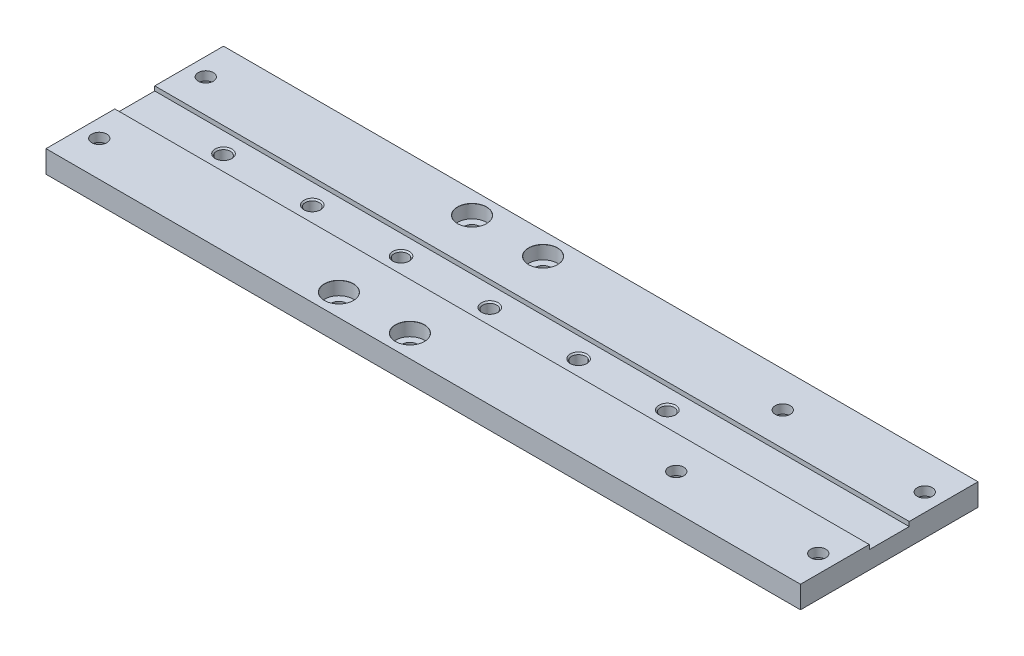
SolidWorks part; units mm, degrees
material "Liga 6061"
ref_plane "Plano frontal" through (0, 0, 0) normal (0, 0, 1) x (1, 0, 0)
ref_plane "Plano superior" through (0, 0, 0) normal (0, 1, 0) x (1, 0, 0)
ref_plane "Plano direito" through (0, 0, 0) normal (1, 0, 0) x (0, 0, -1)
sketch "Esboço1" plane through (0, 0, 0) normal (0, 1, 0) x (1, 0, 0)
  line L1 (85, -20) -> (-85, -20)
  line L2 (85, -20) -> (85, 20)
  line L3 (85, 20) -> (-85, 20)
  line L4 (-85, -20) -> (-85, 20)
  line L5 (85, -20) -> (-85, 20) construction
  line L6 (85, 20) -> (-85, -20) construction
  point P0 (0, 0)
  dimension "D1" = 40
  dimension "D2" = 170
extrude "Ressalto-extrusão1" add sketch "Esboço1" along normal blind 5
sketch "Esboço2" plane through (0, 5, 0) normal (0, 1, 0) x (1, 0, 0)
  line L0 (-85, 20) -> (-85, -20) construction
  line L1 (85, -4.5) -> (-85, -4.5)
  line L2 (85, -4.5) -> (85, 4.5)
  line L3 (85, 4.5) -> (-85, 4.5)
  line L4 (-85, -4.5) -> (-85, 4.5)
  line L5 (85, -4.5) -> (-85, 4.5) construction
  line L6 (85, 4.5) -> (-85, -4.5) construction
  point P0 (0, 0)
  dimension "D1" = 9
extrude "Corte-extrusão1" cut sketch "Esboço2" against normal blind 1
hole_wizard "Rebaixo para SHCS M31" positions "Esboço3" profile "Esboço4" counterbore size "M3" standard "Ansi Metric" end condition through all
sketch "Esboço3" plane through (0, 0, 0) normal (0, -1, 0) x (-1, 0, 0)
  line L0 (-85, -20) -> (-85, 20) construction
  line L1 (-85, 20) -> (85, 20) construction
  line L2 (85, -20) -> (-85, -20) construction
  line L3 (85, 20) -> (85, -20) construction
  point P0 (81, 12)
  point P2 (81, -12)
  point P4 (-49, 12)
  point P6 (-49, -12)
  point P8 (-81, 12)
  point P10 (-81, -12)
  dimension "D1" = 4
  dimension "D2" = 8
  dimension "D3" = 4
  dimension "D4" = 8
  dimension "D5" = 4
  dimension "D6" = 4
  dimension "D7" = 8
  dimension "D8" = 8
  dimension "D9" = 134
  dimension "D10" = 8
  dimension "D11" = 134
  dimension "D12" = 8
sketch "Esboço4" plane through (-81, 0, -12) normal (1, 0, 0) x (0, 0, -1)
  line L0 (0, 0) -> (0, 5)
  line L1 (0, 5) -> (1.7, 5)
  line L3 (1.7, 5) -> (1.7, 3)
  line L4 (3.25, 3) -> (1.7, 3)
  line L5 (3.25, 3) -> (3.25, 0.025)
  line L6 (3.25, 0.025) -> (3.275, 0)
  line L7 (3.275, 0) -> (0, 0)
  line L8 (-3.25, 0.025) -> (-3.275, 0) construction
  line L11 (0, -6.35) -> (0, 107.95) construction
  dimension "Thru Hole Dia." = 3.4
  dimension "Thru Hole Depth" = 5
  dimension "C'Bore Dia." = 6.5
  dimension "C'Bore Depth" = 3
  dimension "Near C'Sink Dia." = 6.55
  dimension "Near C'Sink Angle" = 90
hole_wizard "Rebaixo para SHCS M32" positions "Esboço5" profile "Esboço6" counterbore size "M3" standard "Ansi Metric" end condition through all
sketch "Esboço5" plane through (0, 5, 0) normal (0, 1, 0) x (1, 0, 0)
  line L0 (85, 20) -> (-85, 20) construction
  line L1 (-85, -20) -> (85, -20) construction
  line L2 (-85, 20) -> (-85, 4.5) construction
  line L3 (-85, -4.5) -> (-85, -20) construction
  point P0 (-24, 15)
  point P2 (-8, 15)
  point P4 (-24, -15)
  point P6 (-8, -15)
  dimension "D1" = 5
  dimension "D2" = 5
  dimension "D3" = 5
  dimension "D4" = 5
  dimension "D5" = 61
  dimension "D6" = 61
  dimension "D7" = 16
  dimension "D8" = 16
sketch "Esboço6" plane through (-24, 5, -15) normal (1, 0, 0) x (0, 0, 1)
  line L0 (0, 0) -> (0, 5)
  line L1 (0, 5) -> (1.7, 5)
  line L3 (1.7, 5) -> (1.7, 3)
  line L4 (3.25, 3) -> (1.7, 3)
  line L5 (3.25, 3) -> (3.25, 0.025)
  line L6 (3.25, 0.025) -> (3.275, 0)
  line L7 (3.275, 0) -> (0, 0)
  line L8 (-3.25, 0.025) -> (-3.275, 0) construction
  line L11 (0, -6.35) -> (0, 107.95) construction
  dimension "Thru Hole Dia." = 3.4
  dimension "Thru Hole Depth" = 5
  dimension "C'Bore Dia." = 6.5
  dimension "C'Bore Depth" = 3
  dimension "Near C'Sink Dia." = 6.55
  dimension "Near C'Sink Angle" = 90
hole_wizard "Furo roscado para conduíte de M3x0.51" positions "Esboço7" profile "Esboço8" tap size "M3x0.5" standard "Helicoil® Metric" end condition through all
sketch "Esboço7" plane through (0, 4, 0) normal (0, 1, 0) x (1, 0, 0)
  line L0 (-85, 4.5) -> (-85, -4.5) construction
  point P0 (-65, 0)
  point P2 (-45, 0)
  point P4 (-25, 0)
  point P6 (35, 0)
  point P8 (-5, 0)
  point P10 (15, 0)
  point P15 (6.1987, -1.0944)
  point P16 (12.9533, 0)
  point P17 (5.3272, 0)
  dimension "D1" = 20
  dimension "D2" = 20
  dimension "D3" = 20
  dimension "D4" = 20
  dimension "D5" = 20
  dimension "D6" = 20
sketch "Esboço8" plane through (-65, 4, 0) normal (1, 0, 0) x (0, 0, 1)
  line L0 (0, 0) -> (0, 4)
  line L1 (0, 4) -> (1.575, 4)
  line L2 (1.575, 4) -> (1.575, 0.308)
  line L3 (1.575, 0.308) -> (1.883, 0)
  line L5 (1.883, 0) -> (0, 0)
  line L6 (-1.575, 0.308) -> (-1.883, 0) construction
  line L11 (0, -6.35) -> (0, 107.95) construction
  dimension "Thru Tap Drill Dia." = 3.15
  dimension "Thru Tap Drill Depth" = 4
  dimension "Near C'Sink Dia." = 3.766
  dimension "Near C'Sink Angle" = 90
cosmetic thread "Rosca de furo1" parameters "D1"=3.5, "D2"=3.716
cosmetic thread "Rosca de furo2" parameters "D1"=3.5, "D2"=3.716
cosmetic thread "Rosca de furo3" parameters "D1"=3.5, "D2"=3.716
cosmetic thread "Rosca de furo4" parameters "D1"=3.5, "D2"=3.716
cosmetic thread "Rosca de furo5" parameters "D1"=3.5, "D2"=3.716
cosmetic thread "Rosca de furo6" parameters "D1"=3.5, "D2"=3.716
